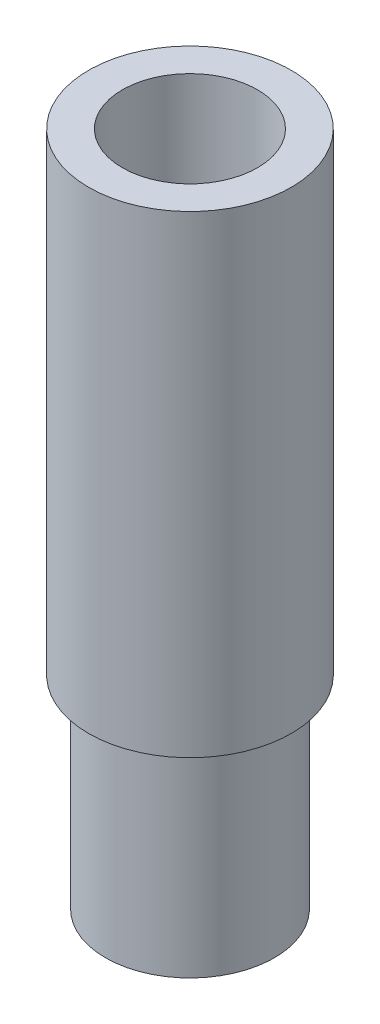
SolidWorks part; units mm, degrees
ref_plane "Front Plane" through (0, 0, 0) normal (0, 0, 1) x (1, 0, 0)
ref_plane "Top Plane" through (0, 0, 0) normal (0, 1, 0) x (1, 0, 0)
ref_plane "Right Plane" through (0, 0, 0) normal (1, 0, 0) x (0, 0, -1)
sketch "Sketch1" plane through (0, 0, 0) normal (0, 1, 0) x (1, 0, 0)
  circle A0 centre (0, 0) radius 6.25
  dimension "D1" = 12.5
extrude "Boss-Extrude1" add sketch "Sketch1" along normal blind 15 contours A0
sketch "Sketch3" plane through (0, 15, 0) normal (0, 1, 0) x (1, 0, 0)
  circle A0 centre (0, 0) radius 7.5
  dimension "D1" = 15
extrude "Boss-Extrude2" add sketch "Sketch3" along normal blind 35 contours A0
sketch "Sketch4" plane through (0, 50, 0) normal (0, 1, 0) x (1, 0, 0)
  circle A0 centre (0, 0) radius 5
  dimension "D1" = 10
extrude "Cut-Extrude1" cut sketch "Sketch4" against normal blind 25
sketch "Sketch5" plane through (0, 0, 0) normal (0, -1, 0) x (-1, 0, 0)
  circle A0 centre (0, 0) radius 2.5
  dimension "D1" = 5
extrude "Cut-Extrude2" cut sketch "Sketch5" against normal blind 35
